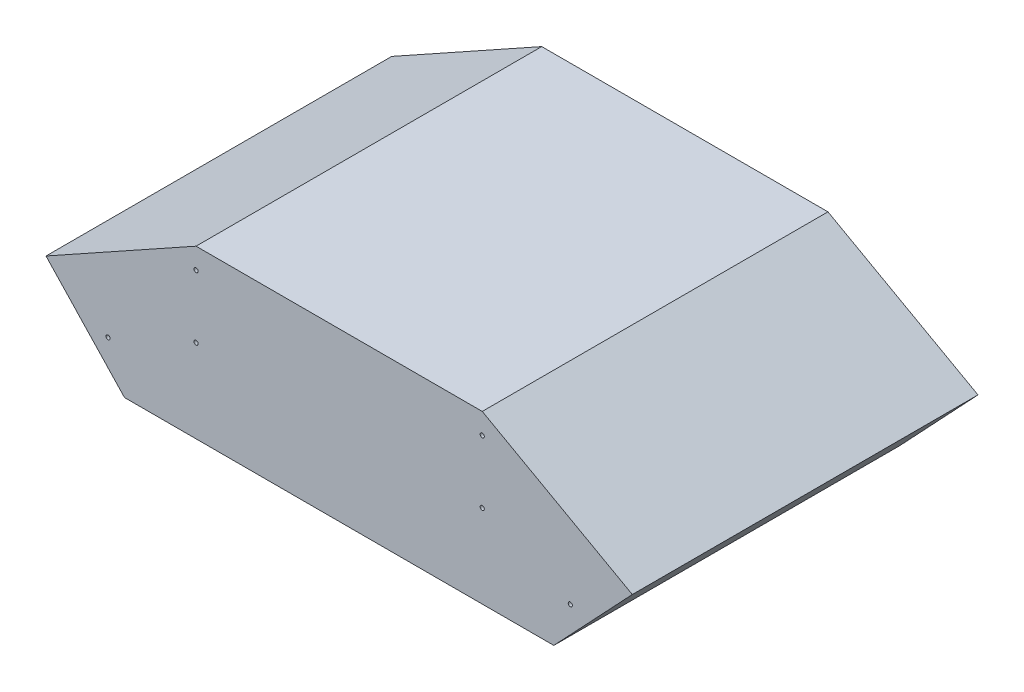
SolidWorks part; units mm, degrees
material "铸造合金钢"
ref_plane "前视基准面" through (0, 0, 0) normal (0, 0, 1) x (1, 0, 0)
ref_plane "上视基准面" through (0, 0, 0) normal (0, 1, 0) x (1, 0, 0)
ref_plane "右视基准面" through (0, 0, 0) normal (1, 0, 0) x (0, 0, -1)
sketch "草图1" plane through (0, 0, 0) normal (0, 0, 1) x (1, 0, 0)
  line L0 (-20.6985, 0) -> (20.6985, 0)
  line L1 (-31.0478, -24.1355) -> (31.0478, -24.1355)
  line L2 (-20.6985, 0) -> (-42.4007, -12.0812)
  line L3 (-31.0478, -24.1355) -> (-42.4007, -12.0812)
  line L4 (0, 5.1055) -> (0, -27.0105)
  line L5 (31.0478, -24.1355) -> (42.4007, -12.0812)
  line L6 (20.6985, 0) -> (42.4007, -12.0812)
  circle A0 centre (-20.6985, -12.0812) radius 0.8279
  circle A1 centre (-20.6985, -12.0812) radius 0.3
  circle A2 centre (-20.6985, -3) radius 0.8279
  circle A3 centre (-20.6985, -3) radius 0.3
  circle A4 centre (-33.4317, -17.7969) radius 1
  circle A5 centre (-33.4317, -17.7969) radius 0.3
  circle A6 centre (33.4317, -17.7969) radius 0.3
  circle A7 centre (33.4317, -17.7969) radius 1
  circle A8 centre (20.6985, -12.0812) radius 0.8279
  circle A9 centre (20.6985, -12.0812) radius 0.3
  circle A10 centre (20.6985, -3) radius 0.3
  circle A11 centre (20.6985, -3) radius 0.8279
  point P5 (0, -24.1355)
extrude "凸台-拉伸3" add sketch "草图1" along normal blind 50 contours A2 A3 | A0 A1 | A4 A5 | A11 A10 | A8 A9 | A7 A6 | L6 L0 L4 L1 L5 A7 A8 A11 | L4 L0 L2 L3 L1 A4 A2 A0
sketch "草图2" plane through (0, 0, 0) normal (0, 1, 0) x (1, 0, 0)
  line L0 (0, -50) -> (0, 0)
  line L1 (-20.6985, -50) -> (20.6985, -50) construction
sketch "草图3" plane through (0, 0, 50) normal (0, 0, 1) x (1, 0, 0)
  line L0 (0, 0) -> (0, -24.1355)
  line L1 (-31.0478, -24.1355) -> (31.0478, -24.1355) construction
ref_plane "基准面1" through (0, 0, 0) normal (1, 0, 0) x (0, 0, -1)
